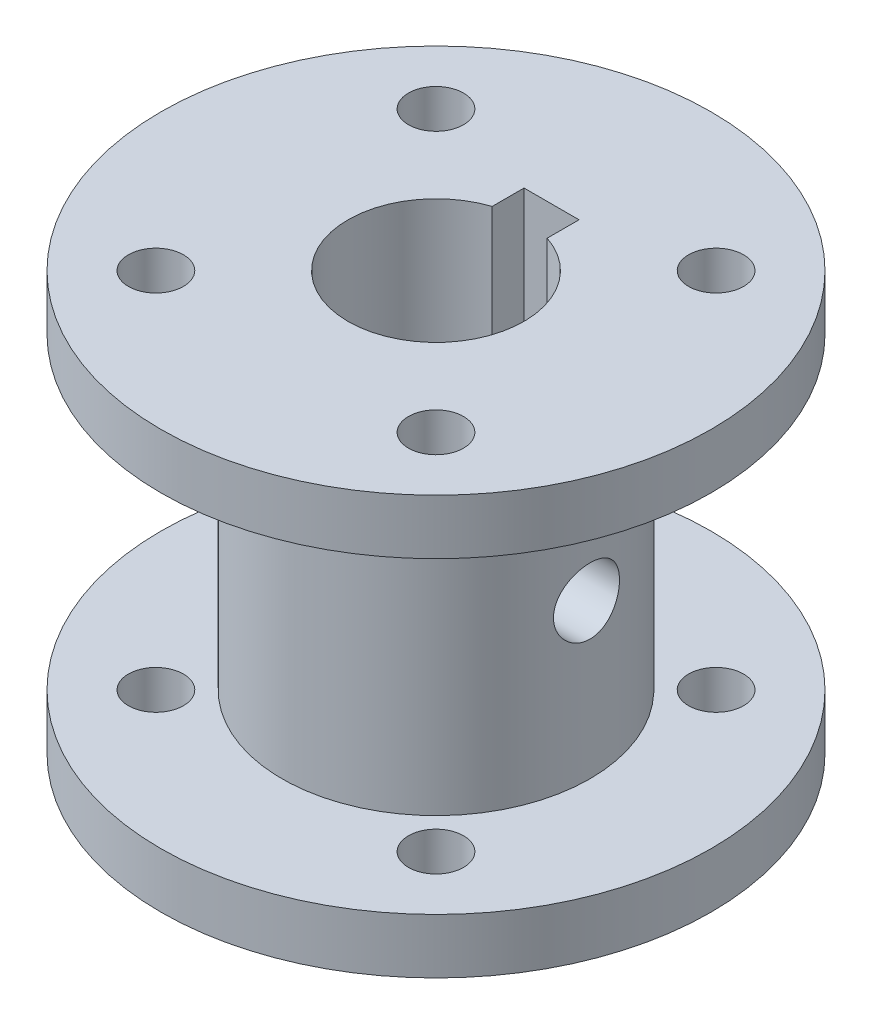
SolidWorks part; units mm, degrees
ref_plane "Front Plane" through (0, 0, 0) normal (0, 0, 1) x (1, 0, 0)
ref_plane "Top Plane" through (0, 0, 0) normal (0, 1, 0) x (1, 0, 0)
ref_plane "Right Plane" through (0, 0, 0) normal (1, 0, 0) x (0, 0, -1)
sketch "Sketch1" plane through (0, 0, 0) normal (0, 0, 1) x (1, 0, 0)
  line L0 (0, -19.1667) -> (0, 19.1667) construction
  line L1 (0, 30.7941) -> (25, 30.7941)
  line L2 (25, 30.7941) -> (25, 25.7941)
  line L3 (25, 25.7941) -> (14, 25.7941)
  line L4 (14, 25.7941) -> (14, -2.2059)
  line L5 (14, -2.2059) -> (25, -2.2059)
  line L6 (25, -2.2059) -> (25, -7.2059)
  line L7 (25, -7.2059) -> (0, -7.2059)
  line L8 (0, -7.2059) -> (0, 30.7941)
  point P1 (0, 0)
  dimension "D1" = 5
  dimension "D2" = 5
  dimension "D3" = 38
  dimension "D4" = 25
  dimension "D5" = 25
  dimension "D6" = 14
revolve "Revolve1" add sketch "Sketch1" angle 360 about L0
sketch "Sketch2" plane through (0, 30.7941, 0) normal (0, 1, 0) x (1, 0, 0)
  line L0 (12.7279, 12.7279) -> (0, 0) construction
  line L1 (0, 0) -> (0, 21) construction
  line L2 (-2.5, 7.5993) -> (-2.5, 10.5)
  line L3 (-2.5, 10.5) -> (2.5, 10.5)
  line L4 (2.5, 7.5993) -> (2.5, 10.5)
  line L5 (0, 8) -> (2.5, 10.5) construction
  line L6 (-2.5, 10.5) -> (0, 8) construction
  circle A0 centre (12.7279, 12.7279) radius 2.5
  circle A1 centre (12.7279, -12.7279) radius 2.5
  circle A2 centre (-12.7279, -12.7279) radius 2.5
  circle A3 centre (-12.7279, 12.7279) radius 2.5
  arc A4 (-2.5, 7.5993) -> (2.5, 7.5993) centre (0, 0) ccw
  point P4 (0, 8)
  point P11 (0, 0)
  point P16 (0, 10.5)
  dimension "D2" = 5
  dimension "D4" = 16
  dimension "D3" = 45
  dimension "D5" = 2.5
  dimension "D6" = 18
  dimension "D7" = 5
  dimension "D1" = 4
extrude "Cut-Extrude1" cut sketch "Sketch2" against normal through all
sketch "Sketch3" plane through (0, 0, 0) normal (1, 0, 0) x (0, 0, -1)
  line L0 (14, -2.2059) -> (-14, -2.2059) construction
  circle A0 centre (0, 11.7941) radius 3
  dimension "D1" = 6
  dimension "D2" = 14
extrude "Cut-Extrude2" cut sketch "Sketch3" against normal through all both and the other way through all
